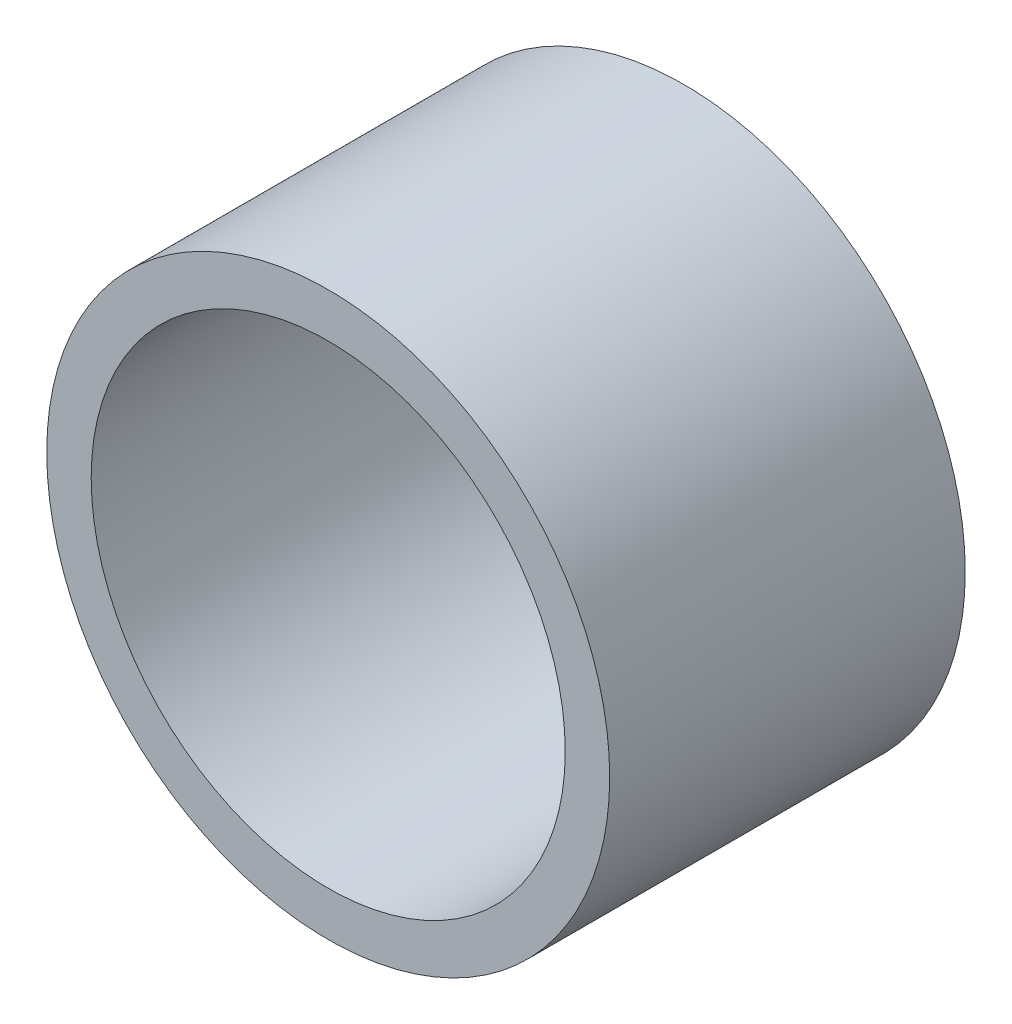
SolidWorks part; units mm, degrees
material "Aluminum Bronze"
ref_plane "Front Plane" through (0, 0, 0) normal (0, 0, 1) x (1, 0, 0)
ref_plane "Top Plane" through (0, 0, 0) normal (0, 1, 0) x (1, 0, 0)
ref_plane "Right Plane" through (0, 0, 0) normal (1, 0, 0) x (0, 0, -1)
sketch "Sketch1" plane through (0, 0, 0) normal (0, 0, 1) x (1, 0, 0)
  circle A0 centre (0, 0) radius 30.1625
  circle A1 centre (0, 0) radius 25.4
  dimension "D1" = 60.325
  dimension "ID" = 50.8
extrude "Extrude1" add sketch "Sketch1" along normal mid plane 38.1
sketch "Sketch2" plane through (0, 0, 0) normal (1, 0, 0) x (0, 0, -1)
  line L0 (-19.05, -25.4) -> (19.05, -25.4) construction
  line L3 (19.05, 25.4) -> (-19.05, 25.4) construction
  line L5 (-19.05, -25.4) -> (19.05, -25.4)
  line L6 (19.05, 25.4) -> (-19.05, 25.4)
sketch "Sketch4" plane through (0, 0, 19.05) normal (0, 0, 1) x (1, 0, 0)
  line L0 (0, 0) -> (-17.9605, 17.9605)
  line L1 (0, -34.925) -> (0, 34.925) construction
  circle A0 centre (0, 0) radius 25.4 construction
  dimension "D1" = 45
